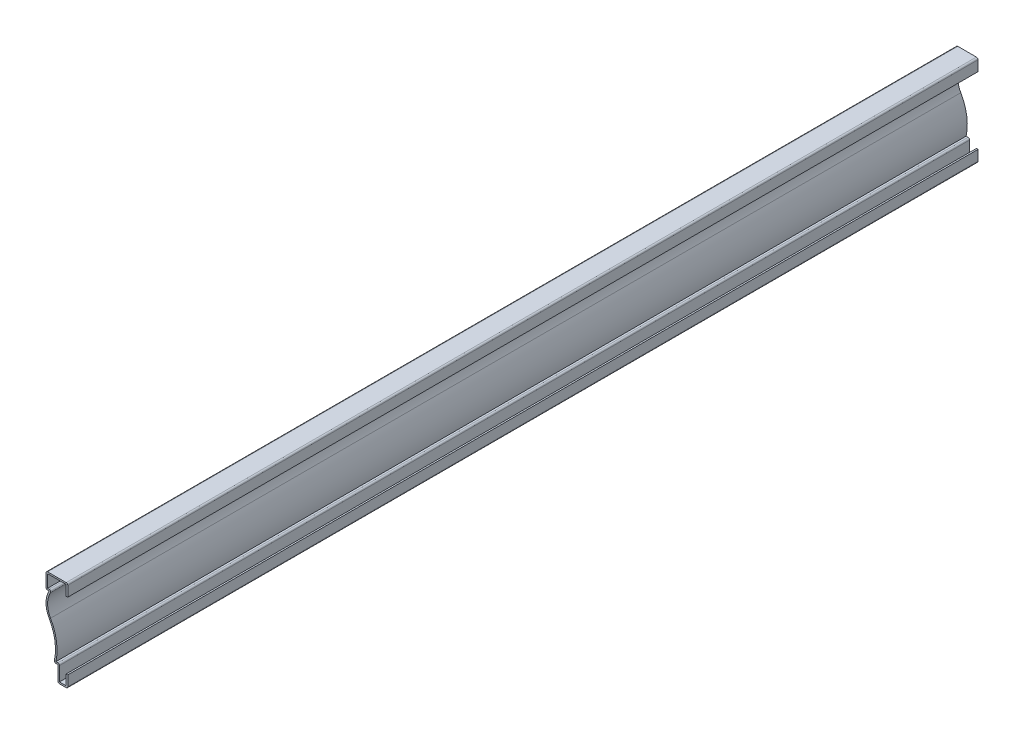
SolidWorks part; units mm, degrees
ref_plane "Front Plane" through (0, 0, 0) normal (0, 0, 1) x (1, 0, 0)
ref_plane "Top Plane" through (0, 0, 0) normal (0, 1, 0) x (1, 0, 0)
ref_plane "Right Plane" through (0, 0, 0) normal (1, 0, 0) x (0, 0, -1)
sketch "Sketch1" plane through (0, 0, 0) normal (0, 0, 1) x (1, 0, 0)
  line L0 (0, 9.525) -> (0, 0)
  line L1 (0, 0) -> (-7.9375, 0)
  line L2 (-7.9375, 0) -> (-7.9375, 12.7)
  line L3 (-7.9375, 12.7) -> (-11.1125, 12.7)
  line L4 (-14.9304, 60.325) -> (-17.4625, 60.325)
  line L5 (-17.4625, 60.325) -> (-17.4625, 73.025)
  line L6 (-17.4625, 73.025) -> (0, 73.025)
  line L7 (0, 73.025) -> (0, 63.5)
  arc A0 (-11.1125, 12.7) -> (-14.9304, 41.3449) centre (-47.9663, 22.3649) ccw
  arc A1 (-14.9304, 41.3449) -> (-14.9304, 60.325) centre (1.5875, 50.835) cw
  point P14 (-9.8902, 13.4628)
  point P15 (0, 0)
  point P16 (-12.5268, 60.325)
  point P17 (0, 0)
  point P18 (-15.3505, 60.325)
  point P19 (-17.4625, 50.835)
  dimension "D9" = 38.1
  dimension "D10" = 19.05
  dimension "D1" = 73.025
  dimension "D2" = 9.525
  dimension "D3" = 9.525
  dimension "D4" = 12.7
  dimension "D5" = 12.7
  dimension "D6" = 17.4625
  dimension "D7" = 3.175
  dimension "D8" = 7.9375
extrude "Extrude-Thin1" add sketch "Sketch1" against normal blind 730.25 thin
fillet "Fillet1" radius 1.27 8 edges at (-17.4625, 60.325, -365.125) (-11.1125, 12.7, -365.125) (-7.9375, 0, -365.125) (-6.6675, 13.97, -365.125) (0, 0, -365.125) (-12.567, 61.595, -365.125) (-17.4625, 73.025, -365.125) (0, 73.025, -365.125)
